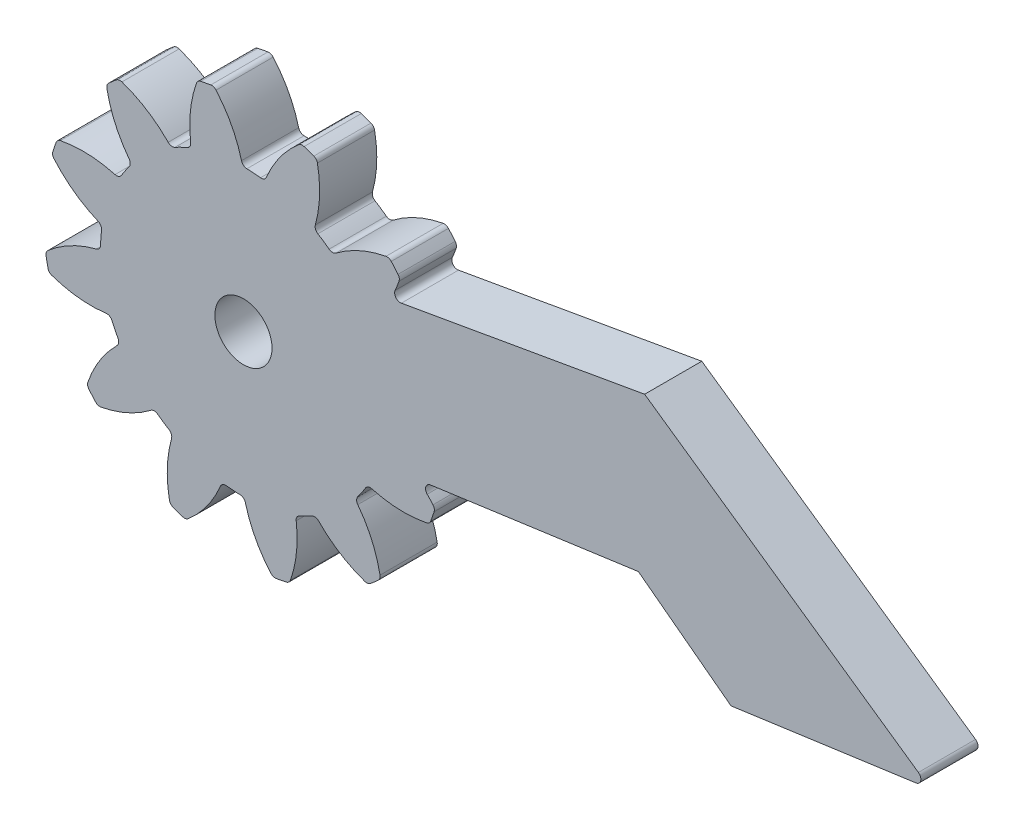
SolidWorks part; units mm, degrees
ref_plane "Plan de face" through (0, 0, 0) normal (0, 0, 1) x (1, 0, 0)
ref_plane "Plan de dessus" through (0, 0, 0) normal (0, 1, 0) x (1, 0, 0)
ref_plane "Plan de droite" through (0, 0, 0) normal (1, 0, 0) x (0, 0, -1)
sketch "Esquisse20" plane through (0, 0, 0) normal (0, 0, 1) x (1, 0, 0)
  line L0 (101.1588, 41.8935) -> (92.8621, 51.4777) construction
  line L1 (101.1588, 41.8935) -> (96.0897, 52.3414) construction
  line L2 (101.1588, 41.8935) -> (91.2539, 48.6042) construction
  line L3 (110.9741, 39.8361) -> (121.8868, 41.3549)
  line L4 (121.8868, 41.3549) -> (126.7495, 37.6805)
  line L5 (126.7495, 37.6805) -> (136.4535, 39.0311)
  line L6 (136.5836, 39.5744) -> (122.2157, 49.5795)
  line L7 (122.2157, 49.5795) -> (109.4461, 47.3346)
  circle A0 centre (101.1588, 41.8935) radius 1.5
  arc A1 (94.4939, 50.0071) -> (94.0838, 49.652) centre (101.1588, 41.8935) ccw
  arc A2 (93.9911, 49.3746) -> (95.1564, 46.7533) centre (100.1325, 50.535) ccw
  arc A3 (95.1576, 46.3919) -> (94.9497, 46.1003) centre (101.1588, 41.8935) ccw
  arc A4 (94.7817, 50.059) -> (97.209, 48.5303) centre (92.7535, 44.1473) cw
  arc A5 (97.8849, 48.6413) -> (97.5666, 48.4773) centre (101.1588, 41.8935) ccw
  arc A6 (95.1564, 46.7533) -> (95.1576, 46.3919) centre (94.9175, 46.5718) cw
  arc A7 (97.209, 48.5303) -> (97.5666, 48.4773) centre (97.4229, 48.7407) ccw
  arc A8 (94.7817, 50.059) -> (94.4939, 50.0071) centre (94.6844, 49.7753) ccw
  arc A9 (93.9911, 49.3746) -> (94.0838, 49.652) centre (94.2859, 49.4303) cw
  arc A10 (98.692, 51.9562) -> (98.3905, 49.1035) centre (104.5907, 49.8905) ccw
  arc A11 (98.3905, 49.1035) -> (98.2108, 48.7898) centre (98.0928, 49.0657) cw
  arc A12 (98.2108, 48.7898) -> (97.8849, 48.6413) centre (101.1588, 41.8935) ccw
  arc A13 (101.6974, 49.3742) -> (101.3397, 49.3914) centre (101.1588, 41.8935) ccw
  arc A14 (101.0566, 49.616) -> (101.3397, 49.3914) centre (101.347, 49.6913) ccw
  arc A15 (99.7188, 52.1536) -> (101.0566, 49.616) centre (95.0065, 48.048) cw
  arc A16 (99.7188, 52.1536) -> (99.4436, 52.2525) centre (99.4926, 51.9565) ccw
  arc A17 (98.692, 51.9562) -> (98.9109, 52.1501) centre (98.9751, 51.857) cw
  arc A18 (99.4436, 52.2525) -> (98.9109, 52.1501) centre (101.1588, 41.8935) ccw
  arc A19 (104.0538, 51.8415) -> (102.3663, 49.5217) centre (108.1294, 47.1031) ccw
  arc A20 (102.3663, 49.5217) -> (102.0539, 49.3399) centre (102.0897, 49.6378) cw
  arc A21 (102.0539, 49.3399) -> (101.6974, 49.3742) centre (101.1588, 41.8935) ccw
  arc A22 (105.3656, 48.1027) -> (105.0644, 48.2964) centre (101.1588, 41.8935) ccw
  arc A23 (104.9315, 48.6325) -> (105.0644, 48.2964) centre (105.2206, 48.5525) ccw
  arc A24 (105.0418, 51.499) -> (104.9315, 48.6325) centre (98.9079, 50.2996) cw
  arc A25 (105.0418, 51.499) -> (104.8529, 51.7223) centre (104.7474, 51.4414) ccw
  arc A26 (104.0538, 51.8415) -> (104.3403, 51.8999) centre (104.2494, 51.614) cw
  arc A27 (104.8529, 51.7223) -> (104.3403, 51.8999) centre (101.1588, 41.8935) ccw
  arc A28 (108.6399, 49.0612) -> (106.0186, 47.896) centre (109.8003, 42.9199) ccw
  arc A29 (106.0186, 47.896) -> (105.6572, 47.8948) centre (105.8371, 48.1348) cw
  arc A30 (105.6572, 47.8948) -> (105.3656, 48.1027) centre (101.1588, 41.8935) ccw
  arc A31 (136.4535, 39.0311) -> (136.5836, 39.5744) centre (136.4122, 39.3282) ccw
  arc A32 (110.8027, 39.3275) -> (110.9741, 39.8361) centre (111.0155, 39.5389) cw
  arc A33 (109.3243, 48.2706) -> (109.1202, 47.7523) centre (103.4125, 50.2989) cw
  arc A34 (109.3243, 48.2706) -> (109.2724, 48.5584) centre (109.0405, 48.368) ccw
  arc A35 (108.6399, 49.0612) -> (108.9173, 48.9686) centre (108.6956, 48.7665) cw
  arc A36 (109.2724, 48.5584) -> (108.9173, 48.9686) centre (101.1588, 41.8935) ccw
  arc A37 (109.1202, 47.7523) -> (109.4461, 47.3346) centre (109.3942, 47.6301) ccw
  arc A46 (111.1068, 38.9986) -> (110.8027, 39.3275) centre (106.3684, 34.923) ccw
  arc A49 (107.3679, 37.6868) -> (107.5617, 37.988) centre (101.1588, 41.8935) ccw
  arc A50 (107.8978, 38.1209) -> (107.5617, 37.988) centre (107.8178, 37.8317) ccw
  arc A51 (110.7643, 38.0106) -> (107.8978, 38.1209) centre (109.5649, 44.1444) cw
  arc A52 (110.7643, 38.0106) -> (110.9875, 38.1995) centre (110.7067, 38.305) ccw
  arc A53 (111.1068, 38.9986) -> (111.1652, 38.712) centre (110.8793, 38.8029) cw
  arc A54 (110.9875, 38.1995) -> (111.1652, 38.712) centre (101.1588, 41.8935) ccw
  arc A55 (108.3265, 34.4125) -> (107.1613, 37.0337) centre (102.1852, 33.2521) ccw
  arc A56 (107.1613, 37.0337) -> (107.1601, 37.3952) centre (107.4001, 37.2153) cw
  arc A57 (107.1601, 37.3952) -> (107.3679, 37.6868) centre (101.1588, 41.8935) ccw
  arc A58 (104.4327, 35.1458) -> (104.751, 35.3098) centre (101.1588, 41.8935) ccw
  arc A59 (105.1086, 35.2568) -> (104.751, 35.3098) centre (104.8947, 35.0464) ccw
  arc A60 (107.5359, 33.7281) -> (105.1086, 35.2568) centre (109.5641, 39.6398) cw
  arc A61 (107.5359, 33.7281) -> (107.8237, 33.78) centre (107.6333, 34.0118) ccw
  arc A62 (108.3265, 34.4125) -> (108.2339, 34.1351) centre (108.0317, 34.3568) cw
  arc A63 (107.8237, 33.78) -> (108.2339, 34.1351) centre (101.1588, 41.8935) ccw
  arc A64 (103.6257, 31.8309) -> (103.9272, 34.6836) centre (97.7269, 33.8966) ccw
  arc A65 (103.9272, 34.6836) -> (104.1069, 34.9972) centre (104.2248, 34.7214) cw
  arc A66 (104.1069, 34.9972) -> (104.4327, 35.1458) centre (101.1588, 41.8935) ccw
  arc A67 (100.6202, 34.4129) -> (100.9779, 34.3957) centre (101.1588, 41.8935) ccw
  arc A68 (101.2611, 34.1711) -> (100.9779, 34.3957) centre (100.9707, 34.0958) ccw
  arc A69 (102.5988, 31.6335) -> (101.2611, 34.1711) centre (107.3112, 35.7391) cw
  arc A70 (102.5988, 31.6335) -> (102.874, 31.5346) centre (102.825, 31.8306) ccw
  arc A71 (103.6257, 31.8309) -> (103.4068, 31.637) centre (103.3425, 31.93) cw
  arc A72 (102.874, 31.5346) -> (103.4068, 31.637) centre (101.1588, 41.8935) ccw
  arc A73 (98.2639, 31.9456) -> (99.9513, 34.2654) centre (94.1883, 36.684) ccw
  arc A74 (99.9513, 34.2654) -> (100.2638, 34.4471) centre (100.228, 34.1493) cw
  arc A75 (100.2638, 34.4471) -> (100.6202, 34.4129) centre (101.1588, 41.8935) ccw
  arc A76 (96.9521, 35.6844) -> (97.2532, 35.4907) centre (101.1588, 41.8935) ccw
  arc A77 (97.3861, 35.1546) -> (97.2532, 35.4907) centre (97.097, 35.2346) ccw
  arc A78 (97.2759, 32.2881) -> (97.3861, 35.1546) centre (103.4097, 33.4875) cw
  arc A79 (97.2759, 32.2881) -> (97.4647, 32.0648) centre (97.5703, 32.3456) ccw
  arc A80 (98.2639, 31.9456) -> (97.9773, 31.8871) centre (98.0682, 32.173) cw
  arc A81 (97.4647, 32.0648) -> (97.9773, 31.8871) centre (101.1588, 41.8935) ccw
  arc A82 (93.6777, 34.7259) -> (96.299, 35.8911) centre (92.5173, 40.8672) ccw
  arc A83 (96.299, 35.8911) -> (96.6605, 35.8923) centre (96.4805, 35.6523) cw
  arc A84 (96.6605, 35.8923) -> (96.9521, 35.6844) centre (101.1588, 41.8935) ccw
  arc A85 (94.4111, 38.6197) -> (94.5751, 38.3013) centre (101.1588, 41.8935) ccw
  arc A86 (94.5221, 37.9438) -> (94.5751, 38.3013) centre (94.3117, 38.1576) ccw
  arc A87 (92.9933, 35.5164) -> (94.5221, 37.9438) centre (98.9051, 33.4882) cw
  arc A88 (92.9933, 35.5164) -> (93.0453, 35.2287) centre (93.2771, 35.4191) ccw
  arc A89 (93.6777, 34.7259) -> (93.4004, 34.8185) centre (93.622, 35.0206) cw
  arc A90 (93.0453, 35.2287) -> (93.4004, 34.8185) centre (101.1588, 41.8935) ccw
  arc A91 (91.0962, 39.4267) -> (93.9489, 39.1252) centre (93.1619, 45.3254) ccw
  arc A92 (93.9489, 39.1252) -> (94.2625, 38.9455) centre (93.9867, 38.8276) cw
  arc A93 (94.2625, 38.9455) -> (94.4111, 38.6197) centre (101.1588, 41.8935) ccw
  arc A94 (93.6782, 42.4322) -> (93.661, 42.0745) centre (101.1588, 41.8935) ccw
  arc A95 (93.4364, 41.7913) -> (93.661, 42.0745) centre (93.3611, 42.0817) ccw
  arc A96 (90.8988, 40.4536) -> (93.4364, 41.7913) centre (95.0044, 35.7412) cw
  arc A97 (90.8988, 40.4536) -> (90.7999, 40.1784) centre (91.0958, 40.2274) ccw
  arc A98 (91.0962, 39.4267) -> (90.9023, 39.6456) centre (91.1953, 39.7098) cw
  arc A99 (90.7999, 40.1784) -> (90.9023, 39.6456) centre (101.1588, 41.8935) ccw
  arc A100 (91.2109, 44.7885) -> (93.5307, 43.101) centre (95.9492, 48.8641) ccw
  arc A101 (93.5307, 43.101) -> (93.7124, 42.7886) centre (93.4146, 42.8244) cw
  arc A102 (93.7124, 42.7886) -> (93.6782, 42.4322) centre (101.1588, 41.8935) ccw
  arc A103 (94.9497, 46.1003) -> (94.756, 45.7991) centre (101.1588, 41.8935) ccw
  arc A104 (94.4198, 45.6662) -> (94.756, 45.7991) centre (94.4999, 45.9554) ccw
  arc A105 (91.5534, 45.7765) -> (94.4198, 45.6662) centre (92.7527, 39.6427) cw
  arc A106 (91.5534, 45.7765) -> (91.3301, 45.5876) centre (91.6109, 45.4821) ccw
  arc A107 (91.2109, 44.7885) -> (91.1524, 45.075) centre (91.4383, 44.9841) cw
  arc A108 (91.3301, 45.5876) -> (91.1524, 45.075) centre (101.1588, 41.8935) ccw
  arc A109 (107.9065, 45.1674) -> (107.7426, 45.4858) centre (101.1588, 41.8935) ccw [skipped]
  arc A110 (107.7955, 45.8433) -> (107.7426, 45.4858) centre (108.0059, 45.6295) ccw [skipped]
  arc A111 (111.2215, 44.3604) -> (108.3688, 44.6619) centre (109.1557, 38.4617) ccw [skipped]
  arc A112 (108.3688, 44.6619) -> (108.0551, 44.8416) centre (108.331, 44.9595) cw [skipped]
  arc A113 (108.0551, 44.8416) -> (107.9065, 45.1674) centre (101.1588, 41.8935) ccw [skipped]
  arc A114 (111.2215, 44.3604) -> (111.4154, 44.1415) centre (111.1223, 44.0773) cw [skipped]
  arc A115 (111.4189, 43.3335) -> (111.5178, 43.6087) centre (111.2218, 43.5597) ccw [skipped]
  arc A116 (111.5178, 43.6087) -> (111.4154, 44.1415) centre (101.1588, 41.8935) ccw [skipped]
  arc A117 (111.4189, 43.3335) -> (108.8813, 41.9958) centre (107.3133, 48.0459) cw [skipped]
  arc A118 (108.6395, 41.3549) -> (108.6566, 41.7126) centre (101.1588, 41.8935) ccw [skipped]
  arc A119 (108.6052, 40.9985) -> (108.6395, 41.3549) centre (101.1588, 41.8935) ccw [skipped]
  arc A120 (108.8813, 41.9958) -> (108.6566, 41.7126) centre (108.9566, 41.7054) ccw [skipped]
  arc A121 (108.787, 40.6861) -> (108.6052, 40.9985) centre (108.9031, 40.9627) cw [skipped]
  point P15 (95.2982, 46.5736)
  point P18 (97.3666, 48.3642)
  point P21 (94.6228, 50.1112)
  point P24 (93.9623, 49.5394)
  point P203 (101.1588, 41.8935)
  dimension "D1" = 3
  dimension "D2" = 21
  dimension "D5" = 12.5
  dimension "D6" = 15
  dimension "D7" = 0.3
  dimension "D9" = 0.3
  dimension "D3" = 15
  dimension "D4" = 15
  dimension "D8" = 12
extrude "Boss.-Extru.18" add sketch "Esquisse20" along normal blind 3 separate body contours A106 A108 A107 A100 A101 A102 A94 A95 A96 A97 A99 A98 A91 A92 A93 A85 A86 A87 A88 A90 A89 A82 A83 A84 A76 A77 A78 A79 A81 A80 A73 A74 A75 A67 A68 A69 A70 A72 A71 A64 A65 A66 A58 A59 A60 A61 A63 A62 A55 A56 A57
